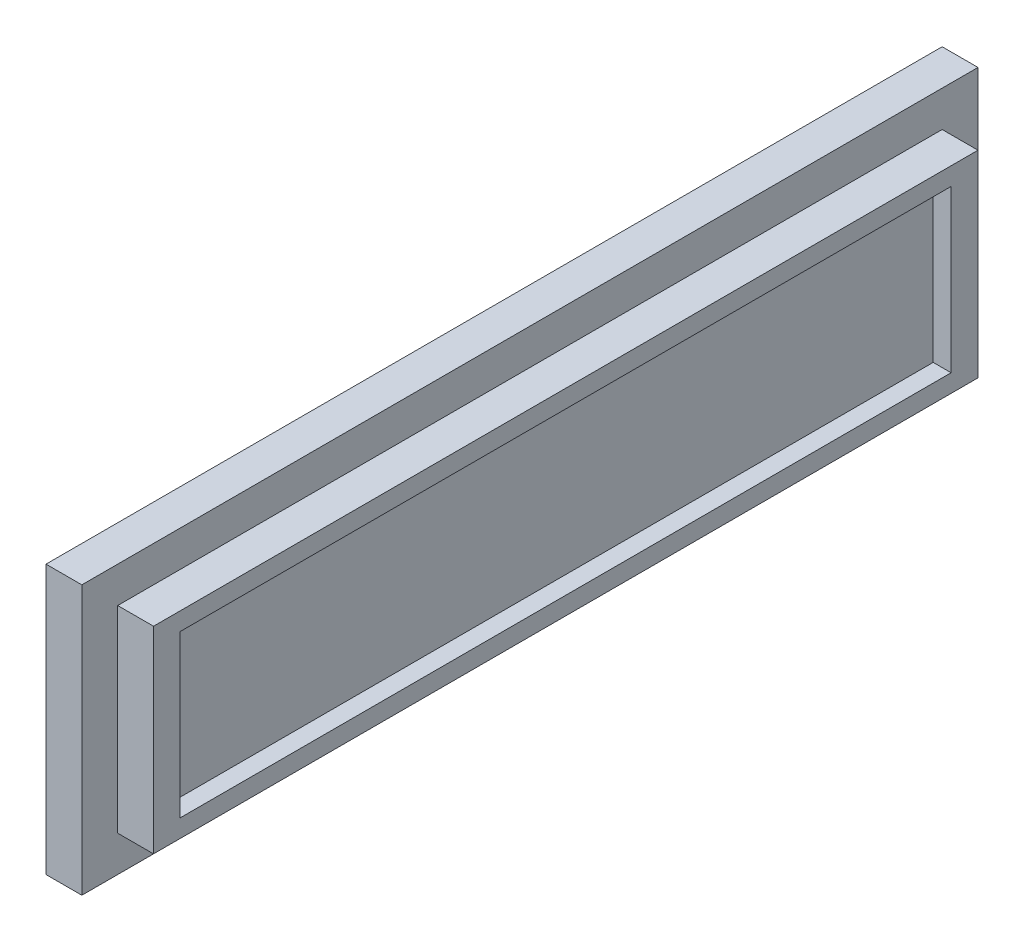
SolidWorks part; units mm, degrees
ref_plane "Front Plane" through (0, 0, 0) normal (0, 0, 1) x (1, 0, 0)
ref_plane "Top Plane" through (0, 0, 0) normal (0, 1, 0) x (1, 0, 0)
ref_plane "Right Plane" through (0, 0, 0) normal (1, 0, 0) x (0, 0, -1)
sketch "Sketch2" plane through (0, 0, 0) normal (1, 0, 0) x (0, 0, -1)
  line L1 (-28.9234, 4.0146) -> (21.0766, 4.0146)
  line L2 (-28.9234, 4.0146) -> (-28.9234, -10.9854)
  line L3 (-28.9234, -10.9854) -> (21.0766, -10.9854)
  line L4 (21.0766, 4.0146) -> (21.0766, -10.9854)
  dimension "D1" = 50
  dimension "D2" = 15
extrude "Boss-Extrude1" add sketch "Sketch2" along normal blind 2
sketch "Sketch4" plane through (2, 0, 0) normal (1, 0, 0) x (0, 0, -1)
  line L0 (-28.9234, 4.0146) -> (-28.9234, -10.9854) construction
  line L1 (-26.9234, 2.0146) -> (19.0766, 2.0146)
  line L2 (-26.9234, 2.0146) -> (-26.9234, -8.9854)
  line L3 (-26.9234, -8.9854) -> (19.0766, -8.9854)
  line L4 (19.0766, 2.0146) -> (19.0766, -8.9854)
  line L5 (21.0766, -10.9854) -> (21.0766, 4.0146) construction
  line L6 (21.0766, 4.0146) -> (-28.9234, 4.0146) construction
  line L7 (-28.9234, -10.9854) -> (21.0766, -10.9854) construction
  dimension "D1" = 2
  dimension "D2" = 2
  dimension "D3" = 2
  dimension "D4" = 2
extrude "Boss-Extrude2" add sketch "Sketch4" along normal blind 2
sketch "Sketch5" plane through (4, 0, 0) normal (1, 0, 0) x (0, 0, -1)
  line L0 (-26.9234, 2.0146) -> (-26.9234, -8.9854) construction
  line L1 (-25.433, 1.0146) -> (17.5766, 1.0146)
  line L2 (-25.433, 1.0146) -> (-25.433, -7.9881)
  line L3 (-25.433, -7.9881) -> (17.5766, -7.9881)
  line L4 (17.5766, 1.0146) -> (17.5766, -7.9881)
  line L5 (19.0766, -8.9854) -> (19.0766, 2.0146) construction
  line L6 (19.0766, 2.0146) -> (-26.9234, 2.0146) construction
  line L7 (-26.9234, -8.9854) -> (19.0766, -8.9854) construction
  dimension "D1" = 1.4903
  dimension "D2" = 1.5
  dimension "D3" = 1
  dimension "D4" = 0.9973
extrude "Cut-Extrude1" cut sketch "Sketch5" against normal blind 1
